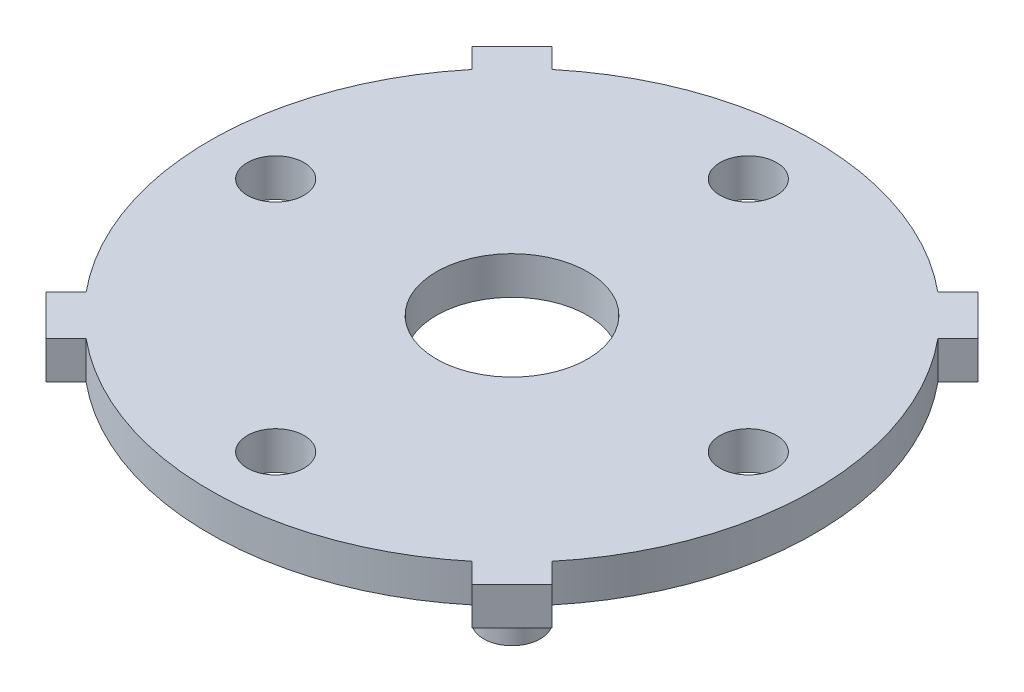
SolidWorks part; units mm, degrees
ref_plane "Front Plane" through (0, 0, 0) normal (0, 0, 1) x (1, 0, 0)
ref_plane "Top Plane" through (0, 0, 0) normal (0, 1, 0) x (1, 0, 0)
ref_plane "Right Plane" through (0, 0, 0) normal (1, 0, 0) x (0, 0, -1)
sketch "Sketch1" plane through (0, 0, 0) normal (0, 1, 0) x (1, 0, 0)
  line L0 (11.2639, 13.3852) -> (13.3852, 11.2639)
  line L1 (13.3852, 11.2639) -> (12.3245, 10.2032)
  line L2 (11.2639, 13.3852) -> (10.2032, 12.3245)
  line L3 (-55, 0) -> (55, 0) construction
  line L4 (13.3852, -11.2639) -> (11.2639, -13.3852)
  line L5 (13.3852, -11.2639) -> (12.3245, -10.2032)
  line L6 (11.2639, -13.3852) -> (10.2032, -12.3245)
  line L7 (-11.2639, -13.3852) -> (-13.3852, -11.2639)
  line L8 (-11.2639, -13.3852) -> (-10.2032, -12.3245)
  line L9 (-13.3852, -11.2639) -> (-12.3245, -10.2032)
  line L10 (-13.3852, 11.2639) -> (-11.2639, 13.3852)
  line L11 (-13.3852, 11.2639) -> (-12.3245, 10.2032)
  line L12 (-11.2639, 13.3852) -> (-10.2032, 12.3245)
  circle A0 centre (0, 0) radius 16
  circle A1 centre (0, 0) radius 4
  circle A2 centre (0, 12.5) radius 1.5
  circle A3 centre (12.5, 0) radius 1.5
  circle A4 centre (0, -12.5) radius 1.5
  circle A5 centre (-12.5, 0) radius 1.5
  point P15 (0, 0)
  point P34 (0, 0)
  dimension "D1" = 32
  dimension "D2" = 8
  dimension "D3" = 3
  dimension "D4" = 12.5
  dimension "D5" = 45
  dimension "D6" = 1.5
  dimension "D7" = 3
extrude "Boss-Extrude1" add sketch "Sketch1" along normal blind 2 contours A0 A5 A4 A3 A2 A1 | A0 L9 L7 L8 | A0 L6 L4 L5 | A0 L1 L0 L2 | A0 L12 L10 L11
sketch "Sketch2" plane through (0, 0, 0) normal (0, -1, 0) x (1, 0, 0)
  line L1 (0, 0) -> (7.0711, 7.0711) construction
  line L2 (1.1, 0) -> (-1.1, 0) construction
  circle A0 centre (7.0711, 7.0711) radius 1.5
  dimension "D1" = 3
  dimension "D2" = 10
  dimension "D3" = 45
extrude "Boss-Extrude2" add sketch "Sketch2" along normal blind 5
equation "\"12i5\"=10.9857"
